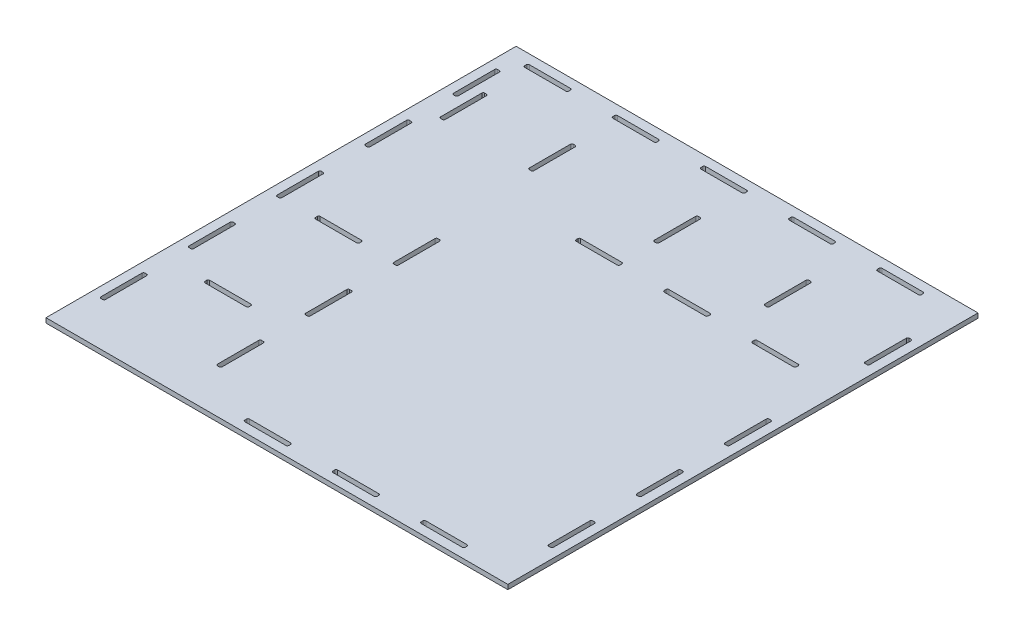
SolidWorks part; units mm, degrees
ref_plane "Front Plane" through (0, 0, 0) normal (0, 0, 1) x (1, 0, 0)
ref_plane "Top Plane" through (0, 0, 0) normal (0, 1, 0) x (1, 0, 0)
ref_plane "Right Plane" through (0, 0, 0) normal (1, 0, 0) x (0, 0, -1)
sketch "Sketch1" plane through (0, 0, 0) normal (0, 1, 0) x (1, 0, 0)
  line L1 (-152.4, -152.4) -> (152.4, -152.4)
  line L2 (-152.4, -152.4) -> (-152.4, 152.4)
  line L3 (-152.4, 152.4) -> (152.4, 152.4)
  line L4 (152.4, -152.4) -> (152.4, 152.4)
  line L5 (-152.4, -152.4) -> (152.4, 152.4) construction
  line L6 (-152.4, 152.4) -> (152.4, -152.4) construction
  point P0 (0, 0)
  dimension "D1" = 304.8
  dimension "D2" = 304.8
extrude "Boss-Extrude1" add sketch "Sketch1" along normal blind 3.175
sketch "Sketch6" plane through (0, 3.175, 0) normal (0, 1, 0) x (1, 0, 0)
  line L0 (-152.4, -152.4) -> (152.4, -152.4) construction
  line L1 (152.4, -152.4) -> (152.4, 152.4) construction
  line L2 (-76.2, -152.4) -> (-73.025, -152.4) construction
  line L3 (-76.2, -152.4) -> (-76.2, 73.025) construction
  line L5 (-73.025, -152.4) -> (-73.025, 73.025) construction
  line L6 (152.4, 73.025) -> (-73.025, 73.025) construction
  line L7 (152.4, 73.025) -> (152.4, 76.2) construction
  line L8 (152.4, 76.2) -> (-76.2, 76.2) construction
  line L9 (-76.2, 73.025) -> (-76.2, 76.2) construction
  line L10 (-152.4, 152.4) -> (-152.4, -152.4) construction
  line L11 (152.4, 152.4) -> (-152.4, 152.4) construction
  line L12 (-76.2, -62.4) -> (-76.2, -32.4)
  line L13 (-76.2, -122.4) -> (-73.025, -122.4)
  line L14 (-76.2, -122.4) -> (-76.2, -92.4)
  line L15 (-76.2, -92.4) -> (-73.025, -92.4)
  line L16 (-73.025, -122.4) -> (-73.025, -92.4)
  line L17 (-76.2, -62.4) -> (-73.025, -62.4)
  line L18 (-73.025, -62.4) -> (-73.025, -32.4)
  line L19 (-76.2, -32.4) -> (-73.025, -32.4)
  line L20 (-76.2, -2.4) -> (-76.2, 27.6)
  line L21 (-76.2, -2.4) -> (-73.025, -2.4)
  line L22 (-73.025, -2.4) -> (-73.025, 27.6)
  line L23 (-76.2, 27.6) -> (-73.025, 27.6)
  line L24 (62.4, 76.2) -> (62.4, 73.025)
  line L25 (122.4, 76.2) -> (92.4, 76.2)
  line L26 (122.4, 76.2) -> (122.4, 73.025)
  line L27 (122.4, 73.025) -> (92.4, 73.025)
  line L28 (92.4, 76.2) -> (92.4, 73.025)
  line L29 (62.4, 76.2) -> (32.4, 76.2)
  line L30 (32.4, 76.2) -> (32.4, 73.025)
  line L31 (62.4, 73.025) -> (32.4, 73.025)
  line L32 (2.4, 76.2) -> (2.4, 73.025)
  line L33 (2.4, 76.2) -> (-27.6, 76.2)
  line L34 (-27.6, 76.2) -> (-27.6, 73.025)
  line L35 (2.4, 73.025) -> (-27.6, 73.025)
  line L36 (152.4, -146.05) -> (-73.025, -146.05) construction
  line L37 (146.05, 73.025) -> (146.05, -146.05) construction
  line L38 (144.4625, -116.05) -> (144.4625, -146.05) construction
  line L39 (116.05, -146.05) -> (86.05, -146.05)
  line L40 (116.05, -146.05) -> (116.05, -142.875)
  line L41 (116.05, -142.875) -> (86.05, -142.875)
  line L42 (86.05, -146.05) -> (86.05, -142.875)
  line L43 (146.05, -116.05) -> (142.875, -116.05)
  line L44 (146.05, -116.05) -> (146.05, -86.05)
  line L45 (146.05, -86.05) -> (142.875, -86.05)
  line L46 (142.875, -116.05) -> (142.875, -86.05)
  line L47 (116.05, -144.4625) -> (146.05, -144.4625) construction
  line L48 (56.05, -146.05) -> (56.05, -142.875)
  line L49 (56.05, -146.05) -> (26.05, -146.05)
  line L50 (26.05, -146.05) -> (26.05, -142.875)
  line L51 (56.05, -142.875) -> (26.05, -142.875)
  line L52 (-3.95, -146.05) -> (-3.95, -142.875)
  line L53 (-3.95, -146.05) -> (-33.95, -146.05)
  line L54 (-33.95, -146.05) -> (-33.95, -142.875)
  line L55 (-3.95, -142.875) -> (-33.95, -142.875)
  line L56 (116.05, -146.05) -> (56.05, -146.05) construction
  line L57 (146.05, -56.05) -> (146.05, -26.05)
  line L58 (146.05, -56.05) -> (142.875, -56.05)
  line L59 (142.875, -56.05) -> (142.875, -26.05)
  line L60 (146.05, -26.05) -> (142.875, -26.05)
  line L61 (146.05, 3.95) -> (146.05, 33.95)
  line L62 (146.05, 3.95) -> (142.875, 3.95)
  line L63 (142.875, 3.95) -> (142.875, 33.95)
  line L64 (146.05, 33.95) -> (142.875, 33.95)
  line L65 (146.05, -116.05) -> (146.05, -56.05) construction
  point P31 (122.4, 74.6125)
  point P52 (86.05, -144.4625)
  dimension "D1" = 3.175
  dimension "D2" = 3.175
  dimension "D3" = 76.2
  dimension "D4" = 76.2
  dimension "D5" = 30
  dimension "D6" = 30
  dimension "D8" = 30
  dimension "D9" = 30
  dimension "D11" = 6.35
  dimension "D12" = 6.35
  dimension "D13" = 3.175
  dimension "D14" = 30
  dimension "D15" = 3.175
  dimension "D16" = 30
  dimension "D17" = 30
  dimension "D18" = 30
  dimension "D20" = 60
  dimension "D22" = 60
  dimension "D7" = 3
  dimension "D10" = 3
  dimension "D19" = 3
  dimension "D21" = 3
extrude "Cut-Extrude4" cut sketch "Sketch6" against normal through all contours L20 L23 L22 L21 | L12 L19 L18 L17 | L14 L13 L16 L15 | L26 L25 L28 L27 | L24 L31 L30 L29 | L32 L35 L34 L33 | L52 L55 L54 L53 | L48 L51 L50 L49 | L40 L39 L42 L41 | L61 L64 L63 L62 | L57 L60 L59 L58 | L44 L43 L46 L45
sketch "Sketch7" plane through (0, 3.175, 0) normal (0, 1, 0) x (1, 0, 0)
  line L0 (-152.4, -152.4) -> (152.4, -152.4) construction
  line L1 (-76.2, 114.3) -> (-152.4, 114.3) construction
  line L4 (-129.3, -77.7875) -> (-99.3, -77.7875)
  line L5 (-129.3, -77.7875) -> (-129.3, -74.6125)
  line L6 (-129.3, -74.6125) -> (-99.3, -74.6125)
  line L7 (-99.3, -77.7875) -> (-99.3, -74.6125)
  line L8 (-129.3, -77.7875) -> (-99.3, -74.6125) construction
  line L9 (-129.3, -74.6125) -> (-99.3, -77.7875) construction
  line L12 (-76.2, -76.2) -> (-152.4, -76.2) construction
  line L13 (-152.4, 152.4) -> (-152.4, -152.4) construction
  line L16 (-129.3, -2.5625) -> (-99.3, -2.5625)
  line L17 (-99.3, 0.6125) -> (-99.3, -2.5625)
  line L18 (-129.3, 0.6125) -> (-99.3, 0.6125)
  line L19 (-129.3, 0.6125) -> (-129.3, -2.5625)
  line L26 (76.2, 152.4) -> (76.2, 76.2) construction
  line L27 (152.4, 152.4) -> (-152.4, 152.4) construction
  line L28 (152.4, -152.4) -> (152.4, 152.4) construction
  line L30 (74.6125, 99.3) -> (77.7875, 99.3)
  line L31 (74.6125, 99.3) -> (74.6125, 129.3)
  line L32 (74.6125, 129.3) -> (77.7875, 129.3)
  line L33 (77.7875, 99.3) -> (77.7875, 129.3)
  line L34 (74.6125, 99.3) -> (77.7875, 129.3) construction
  line L35 (74.6125, 129.3) -> (77.7875, 99.3) construction
  line L39 (2.5625, 129.3) -> (-0.6125, 129.3)
  line L40 (-0.6125, 99.3) -> (-0.6125, 129.3)
  line L41 (2.5625, 99.3) -> (-0.6125, 99.3)
  line L42 (2.5625, 99.3) -> (2.5625, 129.3)
  line L47 (-146.05, 82.55) -> (-146.05, 114.3) construction
  line L48 (-146.05, 82.55) -> (-82.55, 82.55) construction
  line L49 (-146.05, 114.3) -> (-146.05, 146.05) construction
  line L50 (-146.05, 146.05) -> (-82.55, 146.05) construction
  line L51 (-82.55, 114.3) -> (-82.55, 146.05) construction
  line L52 (-82.55, 82.55) -> (-82.55, 114.3) construction
  line L53 (-114.3, 114.3) -> (-114.3, 119.7664) construction
  line L54 (-82.55, 99.3) -> (-85.725, 99.3)
  line L55 (-82.55, 99.3) -> (-82.55, 129.3)
  line L56 (-82.55, 129.3) -> (-85.725, 129.3)
  line L57 (-85.725, 99.3) -> (-85.725, 129.3)
  line L58 (-146.05, 129.3) -> (-142.875, 129.3)
  line L59 (-142.875, 99.3) -> (-142.875, 129.3)
  line L60 (-146.05, 99.3) -> (-142.875, 99.3)
  line L61 (-146.05, 99.3) -> (-146.05, 129.3)
  line L62 (-123.8217, -2.5625) -> (-123.8217, -74.6125) construction
  point P6 (-114.3, -76.2)
  point P11 (-129.3, -76.2)
  point P14 (-114.3, -76.2)
  point P15 (-99.3, -0.975)
  point P35 (76.2, 114.3)
  point P56 (-114.3, 114.3)
  dimension "D1" = 76.2
  dimension "D2" = 3.175
  dimension "D3" = 30
  dimension "D4" = 76.2
  dimension "D5" = 76.2
  dimension "D6" = 76.2
  dimension "D7" = 30
  dimension "D8" = 3.175
  dimension "D9" = 76.2
  dimension "D10" = 63.5
  dimension "D11" = 38.1
  dimension "D12" = 63.5
  dimension "D13" = 3.175
  dimension "D14" = 6.35
  dimension "D15" = 6.35
  dimension "D16" = 30
  dimension "D17" = 72.05
  dimension "D18" = 3.175
  dimension "D19" = 30
  dimension "D20" = 3.175
  dimension "D21" = 30
  dimension "D22" = 72.05
extrude "Cut-Extrude5" cut sketch "Sketch7" against normal through all
sketch "Sketch9" plane through (0, 0, -152.4) normal (0, 0, -1) x (-1, 0, 0)
  line L1 (-152.4, 3.175) -> (152.4, 3.175)
  line L2 (-152.4, 3.175) -> (-152.4, 0)
  line L3 (-152.4, 0) -> (152.4, 0)
  line L4 (152.4, 3.175) -> (152.4, 0)
extrude "Boss-Extrude2" add sketch "Sketch9" along normal blind 15.175
sketch "Sketch10" plane through (-152.4, 0, 0) normal (-1, 0, 0) x (0, 0, 1)
  line L1 (152.4, 3.175) -> (-167.575, 3.175)
  line L2 (152.4, 3.175) -> (152.4, 0)
  line L3 (152.4, 0) -> (-167.575, 0)
  line L4 (-167.575, 3.175) -> (-167.575, 0)
extrude "Boss-Extrude3" add sketch "Sketch10" along normal blind 9.525
sketch "Sketch11" plane through (0, 3.175, 0) normal (0, 1, 0) x (1, 0, 0)
  line L0 (152.4, 161.225) -> (-161.925, 161.225) construction
  line L1 (152.4, -152.4) -> (152.4, 167.575) construction
  line L2 (-161.925, -152.4) -> (-161.925, 167.575) construction
  line L3 (-161.925, 167.575) -> (152.4, 167.575) construction
  line L4 (62.4, 161.225) -> (62.4, 158.05)
  line L5 (122.4, 161.225) -> (92.4, 161.225)
  line L6 (122.4, 161.225) -> (122.4, 158.05)
  line L7 (122.4, 158.05) -> (92.4, 158.05)
  line L8 (92.4, 161.225) -> (92.4, 158.05)
  line L9 (62.4, 161.225) -> (32.4, 161.225)
  line L10 (32.4, 161.225) -> (32.4, 158.05)
  line L11 (62.4, 158.05) -> (32.4, 158.05)
  line L12 (2.4, 161.225) -> (2.4, 158.05)
  line L13 (2.4, 161.225) -> (-27.6, 161.225)
  line L14 (-27.6, 161.225) -> (-27.6, 158.05)
  line L15 (2.4, 158.05) -> (-27.6, 158.05)
  line L16 (-57.6, 161.225) -> (-57.6, 158.05)
  line L17 (-57.6, 161.225) -> (-87.6, 161.225)
  line L18 (-87.6, 161.225) -> (-87.6, 158.05)
  line L19 (-57.6, 158.05) -> (-87.6, 158.05)
  line L20 (-117.6, 161.225) -> (-117.6, 158.05)
  line L21 (-117.6, 161.225) -> (-147.6, 161.225)
  line L22 (-147.6, 161.225) -> (-147.6, 158.05)
  line L23 (-117.6, 158.05) -> (-147.6, 158.05)
  line L24 (122.4, 161.225) -> (62.4, 161.225) construction
  line L25 (142.875, 33.95) -> (142.875, 167.575) construction
  line L26 (77.7875, 129.3) -> (92.4, 129.3) construction
  line L27 (142.875, 129.3) -> (146.05, 129.3)
  line L28 (142.875, 129.3) -> (142.875, 99.3)
  line L29 (142.875, 99.3) -> (146.05, 99.3)
  line L30 (146.05, 129.3) -> (146.05, 99.3)
  line L31 (77.7875, 129.3) -> (74.6125, 129.3) construction
  line L32 (-155.575, 167.575) -> (-155.575, -152.4) construction
  line L33 (-161.925, -152.4) -> (152.4, -152.4) construction
  line L34 (-155.575, -62.4) -> (-155.575, -32.4)
  line L35 (-155.575, -122.4) -> (-152.4, -122.4)
  line L36 (-155.575, -122.4) -> (-155.575, -92.4)
  line L37 (-155.575, -92.4) -> (-152.4, -92.4)
  line L38 (-152.4, -122.4) -> (-152.4, -92.4)
  line L39 (-155.575, -62.4) -> (-152.4, -62.4)
  line L40 (-152.4, -62.4) -> (-152.4, -32.4)
  line L41 (-155.575, -32.4) -> (-152.4, -32.4)
  line L42 (-155.575, -2.4) -> (-155.575, 27.6)
  line L43 (-155.575, -2.4) -> (-152.4, -2.4)
  line L44 (-152.4, -2.4) -> (-152.4, 27.6)
  line L45 (-155.575, 27.6) -> (-152.4, 27.6)
  line L46 (-155.575, 57.6) -> (-155.575, 87.6)
  line L47 (-155.575, 57.6) -> (-152.4, 57.6)
  line L48 (-152.4, 57.6) -> (-152.4, 87.6)
  line L49 (-155.575, 87.6) -> (-152.4, 87.6)
  line L50 (-155.575, 117.6) -> (-155.575, 147.6)
  line L51 (-155.575, 117.6) -> (-152.4, 117.6)
  line L52 (-152.4, 117.6) -> (-152.4, 147.6)
  line L53 (-155.575, 147.6) -> (-152.4, 147.6)
  line L54 (-155.575, -122.4) -> (-155.575, -62.4) construction
  dimension "D1" = 6.35
  dimension "D2" = 30
  dimension "D3" = 30
  dimension "D4" = 3.175
  dimension "D6" = 60
  dimension "D7" = 3.175
  dimension "D8" = 30
  dimension "D9" = 6.35
  dimension "D10" = 3.175
  dimension "D11" = 30
  dimension "D12" = 30
  dimension "D14" = 60
  dimension "D5" = 5
  dimension "D13" = 5
extrude "Cut-Extrude7" cut sketch "Sketch11" against normal through all
fillet "Fillet1" radius 1 91 edges at (122.4, 1.5875, -158.05) (122.4, 1.5875, -161.225) (92.4, 1.5875, -158.05) (92.4, 1.5875, -161.225) (32.4, 1.5875, -161.225) (32.4, 1.5875, -158.05) (62.4, 1.5875, -158.05) (62.4, 1.5875, -161.225) (-27.6, 1.5875, -161.225) (-27.6, 1.5875, -158.05) (2.4, 1.5875, -158.05) (2.4, 1.5875, -161.225) (-57.6, 1.5875, -161.225) (-57.6, 1.5875, -158.05) (-87.6, 1.5875, -158.05) (-87.6, 1.5875, -161.225) (-147.6, 1.5875, -161.225) (-147.6, 1.5875, -158.05) (-117.6, 1.5875, -158.05) (-117.6, 1.5875, -161.225) (-155.575, 1.5875, 2.4) (-152.4, 1.5875, 2.4) (-152.4, 1.5875, -27.6) (-155.575, 1.5875, -27.6) (-129.3, 1.5875, 2.5625) (-129.3, 1.5875, -0.6125) (-99.3, 1.5875, -0.6125) (-76.2, 1.5875, 2.4) (-73.025, 1.5875, 2.4) (-73.025, 1.5875, -27.6) (-76.2, 1.5875, -27.6) (-152.4, 1.5875, -57.6) (-155.575, 1.5875, -117.6) (-152.4, 1.5875, -117.6) (-155.575, 1.5875, -147.6) (-152.4, 1.5875, -147.6) (-142.875, 1.5875, -129.3) (-146.05, 1.5875, -129.3) (-142.875, 1.5875, -99.3) (-85.725, 1.5875, -99.3) (-82.55, 1.5875, -99.3) (-82.55, 1.5875, -129.3) (-0.6125, 1.5875, -129.3) (2.5625, 1.5875, -129.3) (77.7875, 1.5875, -129.3) (77.7875, 1.5875, -99.3) (74.6125, 1.5875, -99.3) (146.05, 1.5875, -99.3) (142.875, 1.5875, -129.3) (142.875, 1.5875, 86.05) (146.05, 1.5875, 86.05) (142.875, 1.5875, 26.05) (142.875, 1.5875, 56.05) (142.875, 1.5875, -3.95) (146.05, 1.5875, -33.95) (122.4, 1.5875, -76.2) (122.4, 1.5875, -73.025) (92.4, 1.5875, -76.2) (92.4, 1.5875, -73.025) (32.4, 1.5875, -73.025) (32.4, 1.5875, -76.2) (62.4, 1.5875, -73.025) (62.4, 1.5875, -76.2) (2.4, 1.5875, -76.2) (2.4, 1.5875, -73.025) (-27.6, 1.5875, -76.2) (-27.6, 1.5875, -73.025) (-76.2, 1.5875, 62.4) (-73.025, 1.5875, 62.4) (-73.025, 1.5875, 92.4) (-76.2, 1.5875, 92.4) (-76.2, 1.5875, 122.4) (-99.3, 1.5875, 74.6125) (-129.3, 1.5875, 74.6125) (-129.3, 1.5875, 77.7875) (-152.4, 1.5875, 122.4) (-155.575, 1.5875, 122.4) (-155.575, 1.5875, 62.4) (-152.4, 1.5875, 62.4) (-155.575, 1.5875, 32.4) (-33.95, 1.5875, 142.875) (-33.95, 1.5875, 146.05) (26.05, 1.5875, 146.05) (26.05, 1.5875, 142.875) (-3.95, 1.5875, 146.05) (56.05, 1.5875, 146.05) (86.05, 1.5875, 142.875) (86.05, 1.5875, 146.05) (116.05, 1.5875, 142.875) (116.05, 1.5875, 146.05) (146.05, 1.5875, 116.05)
